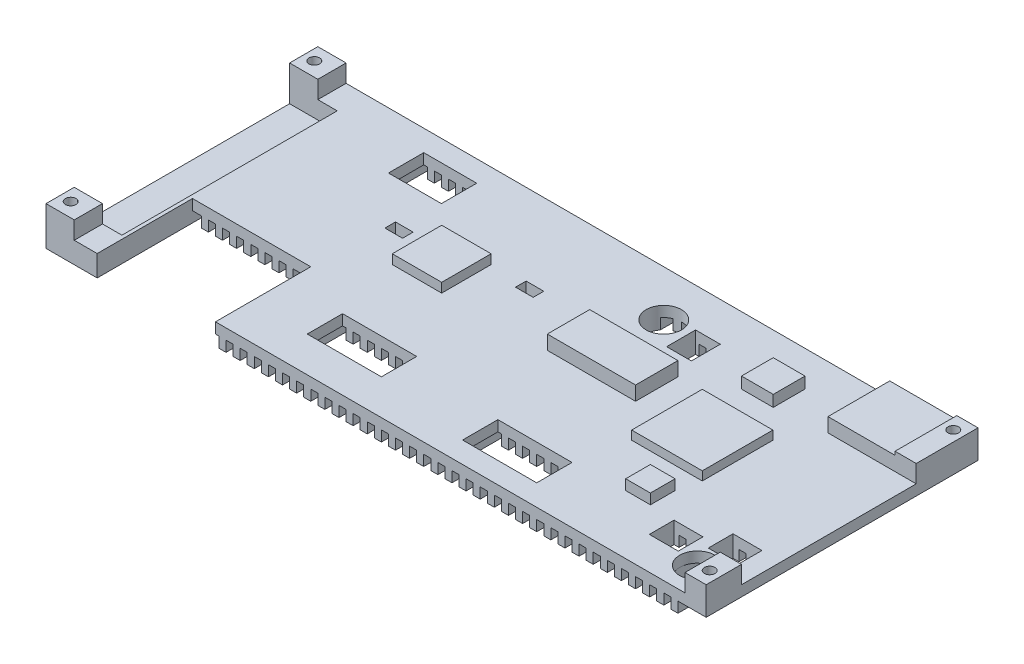
SolidWorks part; units mm, degrees
material "2024 Сплав"
ref_plane "Спереди" through (0, 0, 0) normal (0, 0, 1) x (1, 0, 0)
ref_plane "Сверху" through (0, 0, 0) normal (0, 1, 0) x (1, 0, 0)
ref_plane "Справа" through (0, 0, 0) normal (1, 0, 0) x (0, 0, -1)
sketch "Эскиз1" plane through (0, 0, 0) normal (0, 1, 0) x (1, 0, 0)
  line L1 (0, 77) -> (187, 77)
  line L2 (0, 77) -> (0, 0)
  line L3 (0, 0) -> (187, 0)
  line L4 (187, 77) -> (187, 0)
  dimension "D1" = 187
  dimension "D2" = 77
extrude "Бобышка-Вытянуть1" add sketch "Эскиз1" along normal blind 6
sketch "Эскиз5" plane through (0, 6, 0) normal (0, 1, 0) x (1, 0, 0)
  line L0 (187, 77) -> (0, 77) construction
  line L1 (112, 16) -> (133, 16)
  line L2 (112, 16) -> (112, 6)
  line L3 (112, 6) -> (133, 6)
  line L4 (133, 16) -> (133, 6)
  line L5 (187, 0) -> (187, 77) construction
  line L6 (0, 0) -> (187, 0) construction
  line L7 (36, 71) -> (51, 71)
  line L8 (36, 71) -> (36, 61)
  line L9 (36, 61) -> (51, 61)
  line L10 (51, 71) -> (51, 61)
  line L11 (187, 0) -> (187, 77) construction
  line L12 (64, 20) -> (85, 20)
  line L13 (64, 20) -> (64, 10)
  line L14 (64, 10) -> (85, 10)
  line L15 (85, 20) -> (85, 10)
  line L16 (82, 54) -> (87, 54)
  line L17 (82, 54) -> (82, 51)
  line L18 (82, 51) -> (87, 51)
  line L19 (87, 54) -> (87, 51)
  line L20 (49, 50) -> (54, 50)
  line L21 (49, 50) -> (49, 47)
  line L22 (49, 47) -> (54, 47)
  line L23 (54, 50) -> (54, 47)
  line L24 (14.5, 0) -> (48, 0)
  line L25 (14.5, 0) -> (14.5, 27)
  line L26 (14.5, 27) -> (48, 27)
  line L27 (48, 0) -> (48, 27)
  circle A0 centre (111, 64) radius 5
  circle A1 centre (176, 8.5) radius 5
  dimension "D13" = 10
  dimension "D15" = 10
  dimension "D26" = 139
  dimension "D1" = 54
  dimension "D2" = 6
  dimension "D3" = 10
  dimension "D4" = 21
  dimension "D5" = 136
  dimension "D6" = 6
  dimension "D7" = 15
  dimension "D8" = 10
  dimension "D9" = 10
  dimension "D10" = 21
  dimension "D11" = 102
  dimension "D12" = 10
  dimension "D14" = 11
  dimension "D16" = 76
  dimension "D17" = 100
  dimension "D18" = 5
  dimension "D19" = 3
  dimension "D20" = 23
  dimension "D21" = 3
  dimension "D22" = 5
  dimension "D23" = 27
  dimension "D24" = 133
  dimension "D25" = 8.5
  dimension "D27" = 172.5
  dimension "D28" = 27
  dimension "D29" = 13
extrude "Вырез-Вытянуть2" cut sketch "Эскиз5" against normal through all
sketch "Эскиз7" plane through (0, 0, 0) normal (0, -1, 0) x (1, 0, 0)
  line L0 (48, 0) -> (187, 0) construction
  line L1 (173, 0) -> (175, 0)
  line L2 (173, 0) -> (173, -77)
  line L3 (173, -77) -> (175, -77)
  line L4 (175, 0) -> (175, -77)
  line L5 (187, -77) -> (0, -77) construction
  line L6 (48, -27) -> (14.5, -27) construction
  line L7 (169, 0) -> (171, 0)
  line L8 (169, 0) -> (169, -77)
  line L9 (169, -77) -> (171, -77)
  line L10 (171, 0) -> (171, -77)
  line L11 (161, 0) -> (163, 0)
  line L12 (161, 0) -> (161, -77)
  line L13 (161, -77) -> (163, -77)
  line L14 (163, 0) -> (163, -77)
  line L15 (153, 0) -> (155, 0)
  line L16 (153, 0) -> (153, -77)
  line L17 (153, -77) -> (155, -77)
  line L18 (155, 0) -> (155, -77)
  line L19 (157, 0) -> (159, 0)
  line L20 (157, 0) -> (157, -77)
  line L21 (157, -77) -> (159, -77)
  line L22 (159, 0) -> (159, -77)
  line L23 (149, 0) -> (151, 0)
  line L24 (149, 0) -> (149, -77)
  line L25 (149, -77) -> (151, -77)
  line L26 (151, 0) -> (151, -77)
  line L27 (145, 0) -> (147, 0)
  line L28 (145, 0) -> (145, -77)
  line L29 (145, -77) -> (147, -77)
  line L30 (147, 0) -> (147, -77)
  line L31 (137, 0) -> (139, 0)
  line L32 (137, 0) -> (137, -77)
  line L33 (137, -77) -> (139, -77)
  line L34 (139, 0) -> (139, -77)
  line L35 (141, 0) -> (143, 0)
  line L36 (141, 0) -> (141, -77)
  line L37 (141, -77) -> (143, -77)
  line L38 (143, 0) -> (143, -77)
  line L39 (165, 0) -> (167, 0)
  line L40 (165, 0) -> (165, -77)
  line L41 (165, -77) -> (167, -77)
  line L42 (167, 0) -> (167, -77)
  line L43 (133, 0) -> (135, 0)
  line L44 (133, 0) -> (133, -77)
  line L45 (133, -77) -> (135, -77)
  line L46 (135, 0) -> (135, -77)
  line L47 (129, 0) -> (131, 0)
  line L48 (129, 0) -> (129, -77)
  line L49 (129, -77) -> (131, -77)
  line L50 (131, 0) -> (131, -77)
  line L51 (125, 0) -> (127, 0)
  line L52 (125, 0) -> (125, -77)
  line L53 (125, -77) -> (127, -77)
  line L54 (127, 0) -> (127, -77)
  line L55 (117, 0) -> (119, 0)
  line L56 (117, 0) -> (117, -77)
  line L57 (117, -77) -> (119, -77)
  line L58 (119, 0) -> (119, -77)
  line L59 (121, 0) -> (123, 0)
  line L60 (121, 0) -> (121, -77)
  line L61 (121, -77) -> (123, -77)
  line L62 (123, 0) -> (123, -77)
  line L63 (113, 0) -> (115, 0)
  line L64 (113, 0) -> (113, -77)
  line L65 (113, -77) -> (115, -77)
  line L66 (115, 0) -> (115, -77)
  line L67 (109, 0) -> (111, 0)
  line L68 (109, 0) -> (109, -77)
  line L69 (109, -77) -> (111, -77)
  line L70 (111, 0) -> (111, -77)
  line L71 (105, 0) -> (107, 0)
  line L72 (105, 0) -> (105, -77)
  line L73 (105, -77) -> (107, -77)
  line L74 (107, 0) -> (107, -77)
  line L75 (101, 0) -> (103, 0)
  line L76 (101, 0) -> (101, -77)
  line L77 (101, -77) -> (103, -77)
  line L78 (103, 0) -> (103, -77)
  line L79 (97, 0) -> (99, 0)
  line L80 (97, 0) -> (97, -77)
  line L81 (97, -77) -> (99, -77)
  line L82 (99, 0) -> (99, -77)
  line L87 (95, 0) -> (93, 0)
  line L108 (177, 0) -> (179, 0)
  line L109 (177, 0) -> (177, -77)
  line L110 (177, -77) -> (179, -77)
  line L111 (179, 0) -> (179, -77)
  line L112 (95, 0) -> (95, -77)
  line L113 (95, -77) -> (93, -77)
  line L114 (93, 0) -> (93, -77)
  line L115 (89, 0) -> (91, 0)
  line L116 (89, 0) -> (89, -77)
  line L117 (89, -77) -> (91, -77)
  line L118 (91, 0) -> (91, -77)
  line L119 (85, 0) -> (87, 0)
  line L120 (85, 0) -> (85, -77)
  line L121 (85, -77) -> (87, -77)
  line L122 (87, 0) -> (87, -77)
  line L123 (81, 0) -> (83, 0)
  line L124 (81, 0) -> (81, -77)
  line L125 (81, -77) -> (83, -77)
  line L126 (83, 0) -> (83, -77)
  line L127 (77, 0) -> (79, 0)
  line L128 (77, 0) -> (77, -77)
  line L129 (77, -77) -> (79, -77)
  line L130 (79, 0) -> (79, -77)
  line L131 (73, 0) -> (75, 0)
  line L132 (73, 0) -> (73, -77)
  line L133 (73, -77) -> (75, -77)
  line L134 (75, 0) -> (75, -77)
  line L135 (69, 0) -> (71, 0)
  line L136 (69, 0) -> (69, -77)
  line L137 (69, -77) -> (71, -77)
  line L138 (71, 0) -> (71, -77)
  line L139 (61, 0) -> (63, 0)
  line L140 (61, 0) -> (61, -77)
  line L141 (61, -77) -> (63, -77)
  line L142 (63, 0) -> (63, -77)
  line L143 (65, 0) -> (67, 0)
  line L144 (65, 0) -> (65, -77)
  line L145 (65, -77) -> (67, -77)
  line L146 (67, 0) -> (67, -77)
  line L147 (57, 0) -> (59, 0)
  line L148 (57, 0) -> (57, -77)
  line L149 (57, -77) -> (59, -77)
  line L150 (59, 0) -> (59, -77)
  line L151 (53, 0) -> (55, 0)
  line L152 (53, 0) -> (53, -77)
  line L153 (53, -77) -> (55, -77)
  line L154 (55, 0) -> (55, -77)
  line L155 (49, 0) -> (51, 0)
  line L156 (49, 0) -> (49, -77)
  line L157 (49, -77) -> (51, -77)
  line L158 (51, 0) -> (51, -77)
  line L159 (45, -27) -> (47, -27)
  line L160 (45, -27) -> (45, -77)
  line L161 (45, -77) -> (47, -77)
  line L162 (47, -27) -> (47, -77)
  line L163 (131, -6) -> (131, 23.155) construction
  line L164 (41, -27) -> (43, -27)
  line L165 (41, -27) -> (41, -77)
  line L166 (41, -77) -> (43, -77)
  line L167 (43, -27) -> (43, -77)
  line L168 (37, -27) -> (39, -27)
  line L169 (37, -27) -> (37, -77)
  line L170 (37, -77) -> (39, -77)
  line L171 (39, -27) -> (39, -77)
  line L172 (33, -27) -> (35, -27)
  line L173 (33, -27) -> (33, -77)
  line L174 (33, -77) -> (35, -77)
  line L175 (35, -27) -> (35, -77)
  line L176 (29, -27) -> (31, -27)
  line L177 (29, -27) -> (29, -77)
  line L178 (29, -77) -> (31, -77)
  line L179 (31, -27) -> (31, -77)
  line L180 (25, -27) -> (27, -27)
  line L181 (25, -27) -> (25, -77)
  line L182 (25, -77) -> (27, -77)
  line L183 (27, -27) -> (27, -77)
  line L200 (112, -6) -> (133, -6) construction
  line L202 (21, -27) -> (23, -27)
  line L203 (21, -27) -> (21, -77)
  line L204 (21, -77) -> (23, -77)
  line L205 (23, -27) -> (23, -77)
  line L206 (17, -27) -> (19, -27)
  line L207 (17, -27) -> (17, -77)
  line L208 (17, -77) -> (19, -77)
  line L209 (19, -27) -> (19, -77)
  dimension "D1" = 8
  dimension "D2" = 2
  dimension "D3" = 2
  dimension "D4" = 2
  dimension "D5" = 2
  dimension "D6" = 2
  dimension "D7" = 2
  dimension "D8" = 2
  dimension "D9" = 2
  dimension "D10" = 2
  dimension "D11" = 2
  dimension "D12" = 2
  dimension "D13" = 2
  dimension "D14" = 2
  dimension "D15" = 2
  dimension "D16" = 2
  dimension "D17" = 2
  dimension "D18" = 2
  dimension "D19" = 2
  dimension "D20" = 2
  dimension "D21" = 2
  dimension "D22" = 2
  dimension "D23" = 2
  dimension "D24" = 2
  dimension "D25" = 2
  dimension "D26" = 2
  dimension "D27" = 2
  dimension "D28" = 2
  dimension "D29" = 2
  dimension "D30" = 2
  dimension "D31" = 2
  dimension "D32" = 2
  dimension "D33" = 2
  dimension "D34" = 2
  dimension "D35" = 2
  dimension "D36" = 2
  dimension "D37" = 2
  dimension "D38" = 2
  dimension "D39" = 2
  dimension "D40" = 2
  dimension "D41" = 2
  dimension "D42" = 2
  dimension "D43" = 2
  dimension "D44" = 2
  dimension "D45" = 2
  dimension "D46" = 2
  dimension "D47" = 2
  dimension "D48" = 2
  dimension "D49" = 2
  dimension "D50" = 2
  dimension "D51" = 2
  dimension "D52" = 2
  dimension "D53" = 2
  dimension "D54" = 2
  dimension "D55" = 2
  dimension "D56" = 2
  dimension "D57" = 2
  dimension "D58" = 2
  dimension "D59" = 2
  dimension "D60" = 2
  dimension "D61" = 2
  dimension "D62" = 2
  dimension "D63" = 2
  dimension "D64" = 2
  dimension "D65" = 2
  dimension "D66" = 2
  dimension "D67" = 2
  dimension "D68" = 2
  dimension "D69" = 2
  dimension "D70" = 2
  dimension "D71" = 2
  dimension "D72" = 2
  dimension "D73" = 2
  dimension "D74" = 2
  dimension "D75" = 2
  dimension "D76" = 2
  dimension "D77" = 2
  dimension "D78" = 2
  dimension "D79" = 2
  dimension "D80" = 2
  dimension "D81" = 2
  dimension "D82" = 2
extrude "Вырез-Вытянуть13" cut sketch "Эскиз7" against normal blind 3 flip side to cut
sketch "Эскиз9" plane through (0, 6, 0) normal (0, 1, 0) x (1, 0, 0)
  line L0 (187, 77) -> (0, 77) construction
  line L1 (162, 77) -> (187, 77)
  line L2 (162, 77) -> (162, 59.5)
  line L3 (162, 59.5) -> (187, 59.5)
  line L4 (187, 77) -> (187, 59.5)
  line L5 (187, 0) -> (187, 77) construction
  line L6 (48, 0) -> (187, 0) construction
  line L7 (102, 40) -> (127, 40)
  line L8 (102, 40) -> (102, 52)
  line L9 (102, 52) -> (127, 52)
  line L10 (127, 40) -> (127, 52)
  dimension "D1" = 17.5
  dimension "D2" = 25
  dimension "D3" = 60
  dimension "D4" = 25
  dimension "D5" = 40
  dimension "D6" = 85
extrude "Бобышка-Вытянуть3" add sketch "Эскиз9" along normal blind 4
sketch "Эскиз10" plane through (0, 10, 0) normal (0, 1, 0) x (1, 0, 0)
  line L0 (162, 59.5) -> (187, 59.5) construction
  line L1 (181, 59.5) -> (187, 59.5)
  line L2 (181, 59.5) -> (181, 77)
  line L3 (181, 77) -> (187, 77)
  line L4 (187, 59.5) -> (187, 77)
  dimension "D1" = 6
extrude "Бобышка-Вытянуть7" add sketch "Эскиз10" along normal blind 1
sketch "Эскиз16" plane through (0, 11, 0) normal (0, 1, 0) x (1, 0, 0)
  line L0 (187, 59.5) -> (187, 77) construction
  circle A0 centre (184, 73) radius 1.5
  dimension "D1" = 3
  dimension "D2" = 3
  dimension "D3" = 4
extrude "Вырез-Вытянуть15" cut sketch "Эскиз16" against normal through all
sketch "Эскиз17" plane through (0, 6, 0) normal (0, 1, 0) x (1, 0, 0)
  line L0 (187, 0) -> (187, 59.5) construction
  line L1 (187, 10) -> (181, 10)
  line L2 (187, 10) -> (187, 0)
  line L3 (187, 0) -> (181, 0)
  line L4 (181, 10) -> (181, 0)
  line L5 (48, 0) -> (187, 0) construction
  dimension "D1" = 6
  dimension "D2" = 10
extrude "Бобышка-Вытянуть8" add sketch "Эскиз17" along normal blind 5
sketch "Эскиз18" plane through (0, 11, 0) normal (0, 1, 0) x (1, 0, 0)
  line L0 (181, 0) -> (187, 0) construction
  line L1 (187, 0) -> (187, 10) construction
  circle A0 centre (184, 4) radius 1.5
  dimension "D1" = 4
  dimension "D3" = 3
  dimension "D2" = 3
extrude "Вырез-Вытянуть16" cut sketch "Эскиз18" against normal through all
sketch "Эскиз20" plane through (0, 6, 0) normal (0, 1, 0) x (1, 0, 0)
  line L0 (187, 10) -> (187, 59.5) construction
  line L1 (136, 29.9) -> (156, 29.9)
  line L2 (136, 29.9) -> (136, 49.9)
  line L3 (136, 49.9) -> (156, 49.9)
  line L4 (156, 29.9) -> (156, 49.9)
  line L5 (162, 77) -> (0, 77) construction
  dimension "D1" = 20
  dimension "D2" = 20
  dimension "D3" = 31
  dimension "D4" = 27.1
extrude "Бобышка-Вытянуть9" add sketch "Эскиз20" along normal blind 2.5
sketch "Эскиз21" plane through (0, 6, 0) normal (0, 1, 0) x (1, 0, 0)
  line L0 (187, 10) -> (187, 59.5) construction
  line L1 (173.3, 21.3) -> (181.5, 21.3)
  line L2 (173.3, 21.3) -> (173.3, 14.3)
  line L3 (173.3, 14.3) -> (181.5, 14.3)
  line L4 (181.5, 21.3) -> (181.5, 14.3)
  line L5 (161.6, 16.3) -> (169.8, 16.3)
  line L6 (161.6, 16.3) -> (161.6, 9.3)
  line L7 (161.6, 9.3) -> (169.8, 9.3)
  line L8 (169.8, 16.3) -> (169.8, 9.3)
  line L9 (118, 66) -> (125, 66)
  line L10 (118, 66) -> (118, 57.8)
  line L11 (118, 57.8) -> (125, 57.8)
  line L12 (125, 66) -> (125, 57.8)
  line L13 (48, 0) -> (181, 0) construction
  line L14 (162, 77) -> (0, 77) construction
  dimension "D1" = 8.2
  dimension "D2" = 8.2
  dimension "D3" = 8.2
  dimension "D4" = 7
  dimension "D5" = 7
  dimension "D6" = 5.5
  dimension "D7" = 14.3
  dimension "D8" = 9.3
  dimension "D9" = 7
  dimension "D10" = 62
  dimension "D11" = 11
  dimension "D12" = 17.2
extrude "Вырез-Вытянуть17" cut sketch "Эскиз21" against normal through all
sketch "Эскиз22" plane through (0, 6, 0) normal (0, 1, 0) x (1, 0, 0)
  line L0 (187, 10) -> (187, 59.5) construction
  line L1 (139, 67) -> (148, 67)
  line L2 (139, 67) -> (139, 58)
  line L3 (139, 58) -> (148, 58)
  line L4 (148, 67) -> (148, 58)
  line L5 (162, 77) -> (0, 77) construction
  dimension "D1" = 9
  dimension "D2" = 9
  dimension "D3" = 39
  dimension "D4" = 10
extrude "Бобышка-Вытянуть10" add sketch "Эскиз22" along normal blind 3.2
sketch "Эскиз24" plane through (0, 6, 0) normal (0, 1, 0) x (1, 0, 0)
  line L1 (59, 53.0835) -> (73, 53.0835)
  line L2 (59, 53.0835) -> (59, 39.0835)
  line L3 (59, 39.0835) -> (73, 39.0835)
  line L4 (73, 53.0835) -> (73, 39.0835)
  line L5 (187, 10) -> (187, 59.5) construction
  dimension "D1" = 14
  dimension "D2" = 14
  dimension "D3" = 24
  dimension "D4" = 114
extrude "Бобышка-Вытянуть12" add sketch "Эскиз24" along normal blind 2.65
sketch "Эскиз23" plane through (0, 6, 0) normal (0, 1, 0) x (1, 0, 0)
  line L0 (48, 0) -> (181, 0) construction
  line L1 (147.5, 23.7) -> (154.5, 23.7)
  line L2 (147.5, 23.7) -> (147.5, 16.7)
  line L3 (147.5, 16.7) -> (154.5, 16.7)
  line L4 (154.5, 23.7) -> (154.5, 16.7)
  line L5 (187, 10) -> (187, 59.5) construction
  dimension "D1" = 7
  dimension "D2" = 7
  dimension "D3" = 16.7
  dimension "D4" = 32.5
extrude "Бобышка-Вытянуть11" add sketch "Эскиз23" along normal blind 2.9
sketch "Эскиз25" plane through (0, 3, 0) normal (0, -1, 0) x (1, 0, 0)
  line L0 (0, -77) -> (17, -77) construction
  line L1 (0, 0) -> (14.5, 0)
  line L2 (0, 0) -> (0, -77)
  line L3 (0, -77) -> (14.5, -77)
  line L4 (14.5, 0) -> (14.5, -77)
  dimension "D1" = 14.5
extrude "Бобышка-Вытянуть13" add sketch "Эскиз25" along normal blind 3
sketch "Эскиз26" plane through (0, 6, 0) normal (0, 1, 0) x (1, 0, 0)
  line L0 (0, 77) -> (0, 0) construction
  line L1 (0, 8) -> (13.5, 8)
  line L2 (0, 8) -> (0, 69)
  line L3 (0, 69) -> (13.5, 69)
  line L4 (13.5, 8) -> (13.5, 69)
  dimension "D1" = 13.5
  dimension "D2" = 8
  dimension "D3" = 8
extrude "Вырез-Вытянуть19" cut sketch "Эскиз26" against normal blind 5
sketch "Эскиз27" plane through (0, 6, 0) normal (0, 1, 0) x (1, 0, 0)
  line L0 (0, 0) -> (14.5, 0) construction
  line L1 (0, 8) -> (8, 8)
  line L2 (0, 8) -> (0, 0)
  line L3 (0, 0) -> (8, 0)
  line L4 (8, 8) -> (8, 0)
  line L5 (13.5, 69) -> (0, 69) construction
  line L6 (0, 77) -> (8, 77)
  line L7 (0, 77) -> (0, 69)
  line L8 (0, 69) -> (8, 69)
  line L9 (8, 77) -> (8, 69)
  dimension "D1" = 8
extrude "Бобышка-Вытянуть14" add sketch "Эскиз27" along normal blind 5
sketch "Эскиз28" plane through (0, 11, 0) normal (0, 1, 0) x (1, 0, 0)
  circle A0 centre (3, 4) radius 1.5
  dimension "D1" = 3
  dimension "D2" = 4
  dimension "D3" = 3
extrude "Вырез-Вытянуть20" cut sketch "Эскиз28" against normal through all
sketch "Эскиз29" plane through (0, 11, 0) normal (0, 1, 0) x (1, 0, 0)
  line L0 (0, 77) -> (0, 69) construction
  circle A0 centre (3, 73) radius 1.5
  dimension "D1" = 3
  dimension "D2" = 4
  dimension "D3" = 3
extrude "Вырез-Вытянуть21" cut sketch "Эскиз29" against normal through all
ref_plane "Плоскость48" through (0, 0, 0) normal (-0.1484, -0.7819, 0.6055) x (0.8158, -0.4429, -0.3719)
